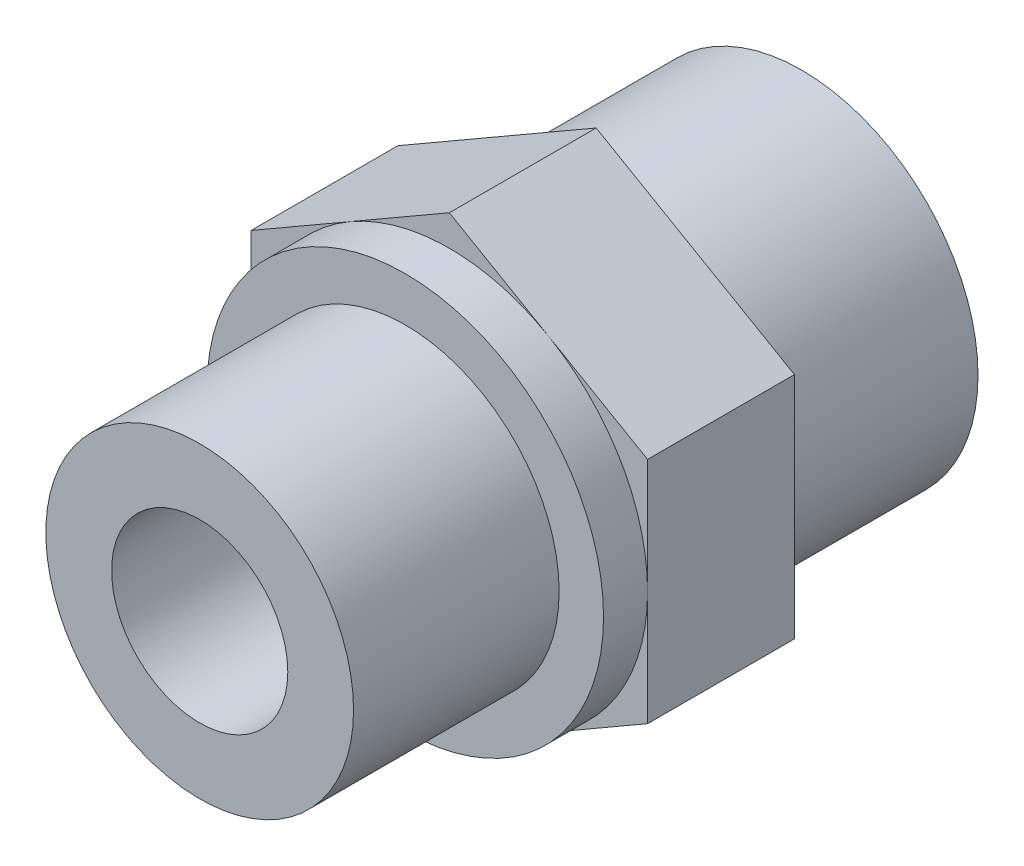
SolidWorks part; units mm, degrees
ref_plane "Plane1" through (0, 0, 0) normal (0, 0, 1) x (1, 0, 0)
ref_plane "Plane2" through (0, 0, 0) normal (0, 1, 0) x (1, 0, 0)
ref_plane "Plane3" through (0, 0, 0) normal (1, 0, 0) x (0, 0, -1)
sketch "Sketch1" plane through (0, 0, 0) normal (0, 0, 1) x (1, 0, 0)
  line L1 (0, 15.5885) -> (-13.5, 7.7942)
  line L2 (-13.5, 7.7942) -> (-13.5, -7.7942)
  line L3 (-13.5, -7.7942) -> (0, -15.5885)
  line L4 (0, -15.5885) -> (13.5, -7.7942)
  line L5 (13.5, -7.7942) -> (13.5, 7.7942)
  line L6 (13.5, 7.7942) -> (0, 15.5885)
  circle A0 centre (0, 0) radius 13.5 construction
  dimension "Nøglevidde" = 27
extrude "Base-Extrude" add sketch "Sketch1" along normal blind 10
sketch "Sketch2" plane through (0, 0, 10) normal (0, 0, 1) x (1, 0, 0)
  circle A0 centre (0, 0) radius 13.5
  dimension "Nøglediameter" = 27
extrude "Boss-Extrude1" add sketch "Sketch2" along normal blind 3
sketch "Sketch3" plane through (0, 0, 13) normal (0, 0, 1) x (1, 0, 0)
  circle A0 centre (0, 0) radius 10.4775
  dimension "RG-Gevind" = 20.955
extrude "Boss-Extrude2" add sketch "Sketch3" along normal blind 14
sketch "Sketch4" plane through (0, 0, 0) normal (0, 0, -1) x (-1, 0, 0)
  circle A0 centre (0, 0) radius 12
  dimension "M-Gevind" = 24
extrude "Boss-Extrude3" add sketch "Sketch4" along normal blind 14
sketch "Sketch5" plane through (0, 0, 27) normal (0, 0, 1) x (1, 0, 0)
  circle A0 centre (0, 0) radius 6
  dimension "D1 (Indv.diameter)" = 12
extrude "Cut-Extrude1" cut sketch "Sketch5" against normal through all
sketch "Sketch7" plane through (0, 0, 0) normal (1, 0, 0) x (0, 0, -1)
  line L0 (0, 0) -> (11.704, 0) construction
  line L1 (-13, 0) -> (-10, 0) construction
  line L2 (14, 0) -> (14, 9.15)
  line L3 (14, -12) -> (14, 12) construction
  line L4 (14, 9.15) -> (8.5897, 8)
  line L5 (8.5897, 8) -> (5.5, 8)
  line L6 (5.5, 8) -> (5.5, 0)
  line L7 (5.5, 0) -> (14, 0)
  dimension "D4" = 18.3
  dimension "D2" = 16
  dimension "D3" = 12
  dimension "L8" = 8.5
revolve "Cut-Revolve1" cut sketch "Sketch7" angle 360 about L0
